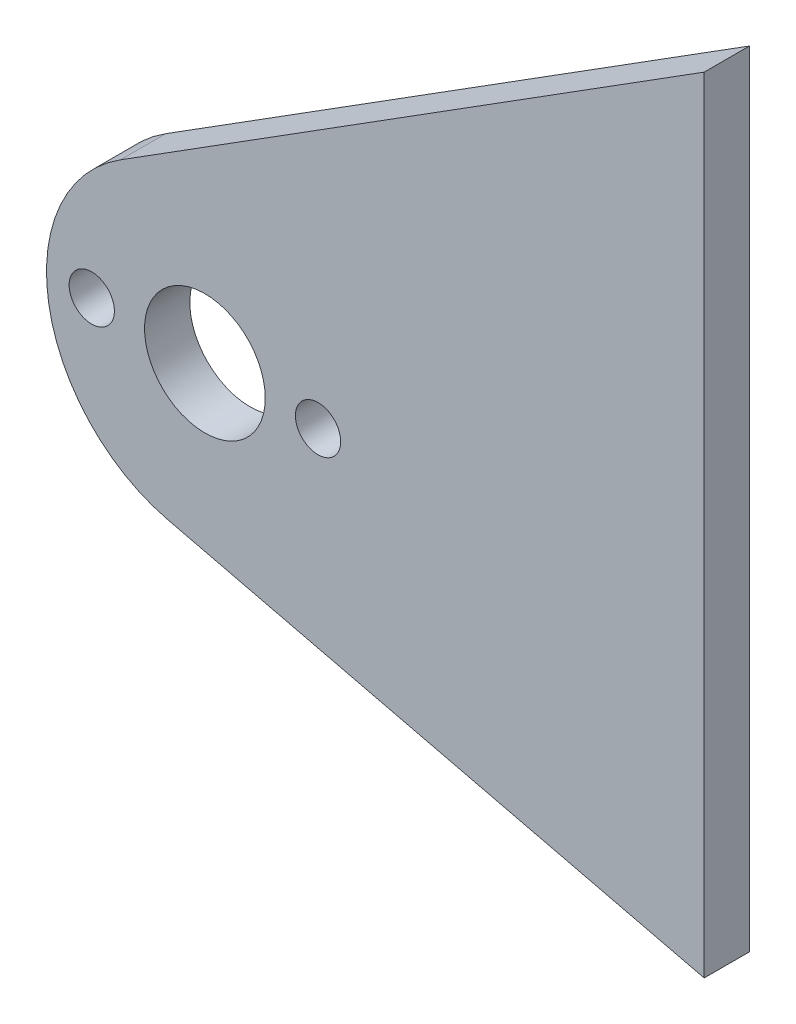
SolidWorks part; units mm, degrees
material "Resina de poliéster"
ref_plane "Alzado" through (0, 0, 0) normal (0, 0, 1) x (1, 0, 0)
ref_plane "Planta" through (0, 0, 0) normal (0, 1, 0) x (1, 0, 0)
ref_plane "Vista lateral" through (0, 0, 0) normal (1, 0, 0) x (0, 0, -1)
sketch "Model" plane through (0, 0, 0) normal (0, 0, 1) x (1, 0, 0)
  line L159 (33.0926, 34.6617) -> (33.0926, 21.7647)
  line L160 (0, 2.8) -> (0, 0) construction
  line L161 (1.4, 1.4) -> (-1.4, 1.4) construction
  line L162 (7.5, 2.9) -> (7.5, -0.1) construction
  line L163 (9, 1.4) -> (6, 1.4) construction
  line L164 (-6, 1.4) -> (-9, 1.4) construction
  line L165 (-7.5, 2.9) -> (-7.5, -0.1) construction
  line L166 (33.0926, 34.6617) -> (33.0926, -17.3383)
  line L167 (33.0926, 34.6617) -> (-5.5974, 10.2836)
  line L168 (33.0926, -17.3383) -> (-2.4499, -8.8102)
  line L240 (-18.0548, 1.4) -> (56.1866, 1.4)
  arc A122 (-5.5974, 10.2836) -> (-2.4499, -8.8102) centre (0, 1.4) ccw
  circle A123 centre (7.5, 1.4) radius 1.5
  circle A124 centre (-7.5, 1.4) radius 1.5
  circle A126 centre (0, 1.4) radius 4
  point P647 (33.0926, 1.4)
  point P648 (6, 1.4)
  point P649 (9, 1.4)
  point P650 (-3.0272, -1.2146)
  point P651 (3.0272, 4.0146)
  dimension "D6" = 4
  dimension "D1" = 52
  dimension "D2" = 18.7383
  dimension "D3" = 3
  dimension "D4" = 33.0926
  dimension "D5" = 25.5926
  dimension "D7" = 8
extrude "Saliente-Extruir1" add sketch "Model" along normal blind 3 contours A126 L240 A123 L166 L159 L167 A122 A124 | A126 L240 A124 A122 L168 L166 A123
